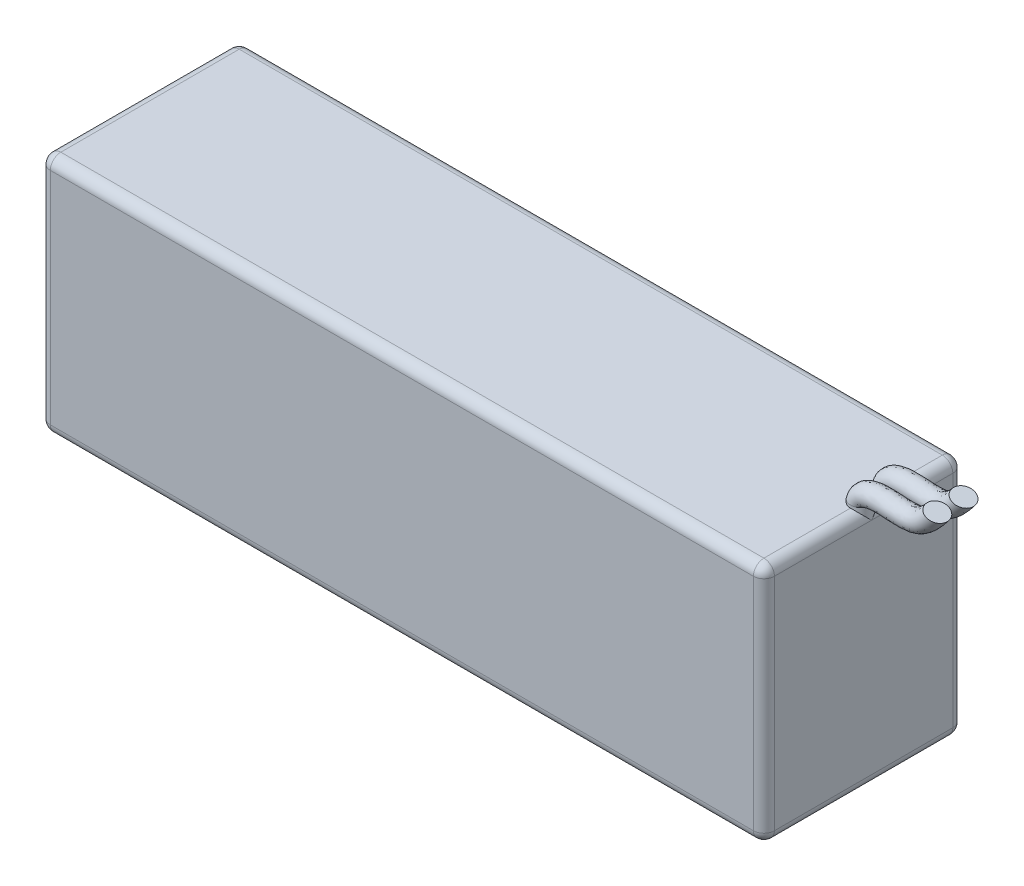
SolidWorks part; units mm, degrees
ref_plane "Płaszczyzna przednia" through (0, 0, 0) normal (0, 0, 1) x (1, 0, 0)
ref_plane "Płaszczyzna górna" through (0, 0, 0) normal (0, 1, 0) x (1, 0, 0)
ref_plane "Płaszczyzna prawa" through (0, 0, 0) normal (1, 0, 0) x (0, 0, -1)
sketch "Szkic1" plane through (0, 0, 0) normal (0, 1, 0) x (1, 0, 0)
  line L1 (-69, -19) -> (69, -19)
  line L2 (-69, -19) -> (-69, 19)
  line L3 (-69, 19) -> (69, 19)
  line L4 (69, -19) -> (69, 19)
  line L5 (-69, -19) -> (69, 19) construction
  line L6 (-69, 19) -> (69, -19) construction
  point P0 (0, 0)
  dimension "D1" = 138
  dimension "D2" = 38
extrude "Dodanie-wyciągnięcie1" add sketch "Szkic1" along normal blind 46
fillet "Zaokrąglenie1" radius 2 12 edges at (0, 0, -19) (0, 0, 19) (0, 46, 19) (0, 46, -19) (-69, 23, -19) (-69, 46, 0) (-69, 23, 19) (-69, 0, 0) (69, 23, 19) (69, 46, 0) (69, 23, -19) (69, 0, 0)
ref_plane "Płaszczyzna1" through (0, 46.5, 0) normal (0, 1, 0) x (1, 0, 0)
sketch "Szkic3" plane through (0, 46.5, 0) normal (0, 1, 0) x (1, 0, 0)
  line L0 (0, 0) -> (67, 0) construction
  line L1 (67, 0) -> (67, 4) construction
  line L2 (67, 1.5) -> (67, 6.5) construction
  circle A0 centre (67, 6.5) radius 2
  circle A1 centre (67, 1.5) radius 2
  point P7 (67, 4)
  point P9 (67, 4)
  dimension "D1" = 5
  dimension "D2" = 4
  dimension "D3" = 4
  dimension "D4" = 67
  dimension "D5" = 4
extrude "Dodanie-wyciągnięcie2" add sketch "Szkic3" against normal up to body
ref_plane "Płaszczyzna2" through (0, 0, -4) normal (0, 0, -1) x (-1, 0, 0)
sketch "Szkic4" plane through (0, 0, -4) normal (0, 0, -1) x (-1, 0, 0)
  line L0 (-65, 46.5) -> (-69, 46.5) construction
  spline S0 degree 3 poles (-67, 46.5) (-67.8123, 48.7) (-76.5581, 48.0536) (-78.812, 48.1963) (-81.5465, 51.6201) knots 0 0 0 0 0.3683 1 1 1 1
sketch "Szkic5" plane through (0, 46.5, 0) normal (0, 1, 0) x (1, 0, 0)
  circle A0 centre (67, 6.5) radius 2
  circle A1 centre (67, 1.5) radius 2
sweep "Wyciągnięcie po ścieżce1" add profiles "Szkic5" path "Szkic4"
